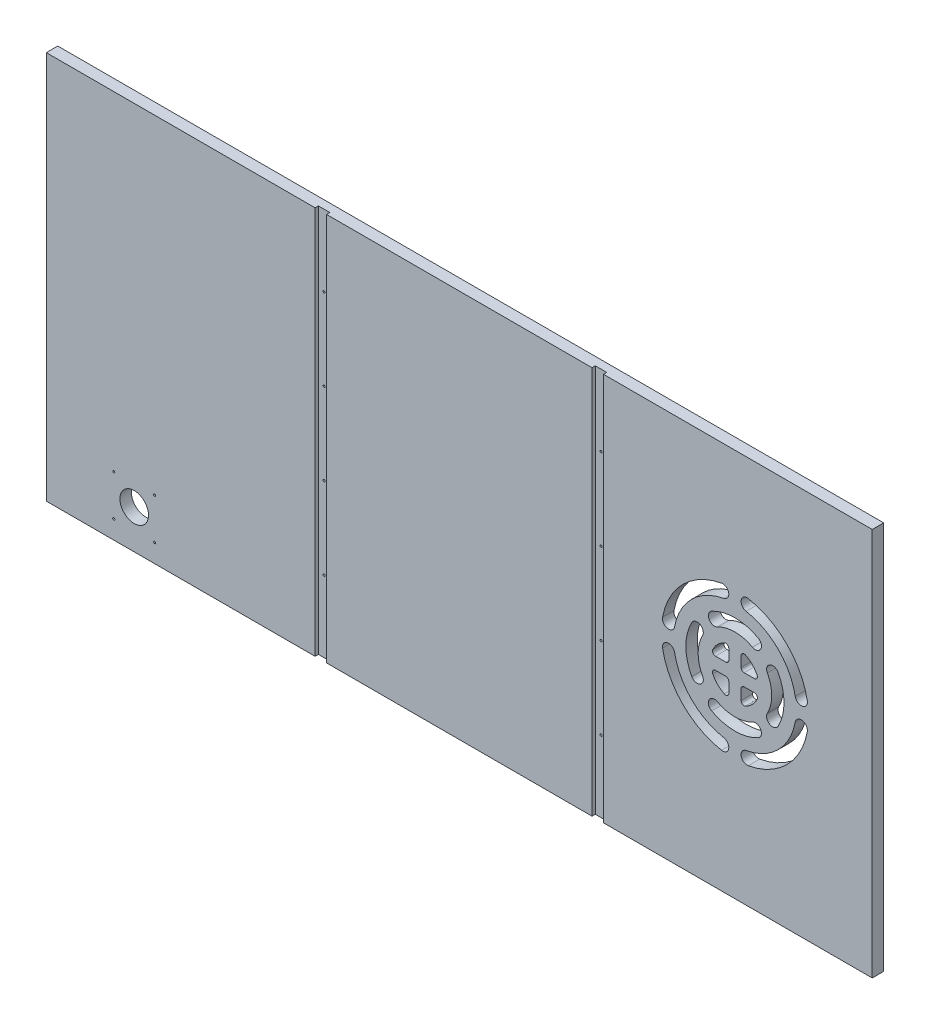
SolidWorks part; units mm, degrees
material "Pine"
ref_plane "Front Plane" through (0, 0, 0) normal (0, 0, 1) x (1, 0, 0)
ref_plane "Top Plane" through (0, 0, 0) normal (0, 1, 0) x (1, 0, 0)
ref_plane "Right Plane" through (0, 0, 0) normal (1, 0, 0) x (0, 0, -1)
sketch "Sketch1" plane through (0, 0, 0) normal (0, 0, 1) x (1, 0, 0)
  line L0 (8932.6508, -5243.5125) -> (10226.1458, -5243.5125)
  line L1 (9086.3208, -4722.0918) -> (10222.9708, -4853.7812)
  line L2 (8914.8708, -6342.0625) -> (10197.5708, -6342.0625)
  line L3 (8914.8708, -5808.6625) -> (10197.5708, -5808.6625)
  line L4 (8919.6333, -5253.0375) -> (10218.2083, -5253.0375)
  line L5 (9134.2633, -4656.1375) -> (9134.2633, -4638.3575)
  line L6 (9091.0833, -4638.3575) -> (9134.2633, -4638.3575)
  line L7 (9091.0833, -4567.2375) -> (9091.0833, -4638.3575)
  line L8 (9134.2633, -4656.1375) -> (9581.3033, -4656.1375)
  line L9 (9091.0833, -4567.2375) -> (9624.4833, -4567.2375)
  line L10 (9581.3033, -4656.1375) -> (9581.3033, -4638.3575)
  line L11 (9581.3033, -4638.3575) -> (9624.4833, -4638.3575)
  line L12 (9624.4833, -4567.2375) -> (9624.4833, -4638.3575)
  line L13 (8932.6508, -5225.7325) -> (9344.9775, -5225.7325)
  line L14 (8932.6508, -5256.2125) -> (8932.6508, -5243.5125)
  line L15 (8911.6958, -5256.2125) -> (8932.6508, -5256.2125)
  line L16 (8914.8708, -4722.0918) -> (9086.3208, -4722.0918)
  line L17 (8911.6958, -4715.5913) -> (8932.6508, -4715.5913)
  line L18 (8914.8708, -6342.0625) -> (8914.8708, -5808.6625)
  line L19 (12082.9917, -4722.0918) -> (10946.3417, -4853.7812)
  line L20 (12236.6617, -5243.5125) -> (10943.1667, -5243.5125)
  line L21 (10951.1042, -5253.0375) -> (12249.6792, -5253.0375)
  line L22 (10838.3917, -5656.2625) -> (11308.2917, -5656.2625)
  line L23 (10838.3917, -5719.7625) -> (11308.2917, -5719.7625)
  line L24 (10838.3917, -5742.5368) -> (11308.2917, -5742.5368)
  line L25 (10806.6417, -6342.0625) -> (11340.0417, -6342.0625)
  line L26 (10803.4667, -6335.7125) -> (11343.2167, -6335.7125)
  line L27 (10803.4667, -6317.9325) -> (11343.2167, -6317.9325)
  line L28 (10943.1667, -5225.7325) -> (11376.4483, -5225.7325)
  line L29 (11506.7292, -4754.5625) -> (10806.6417, -4827.5875)
  line L30 (11506.7292, -4567.2375) -> (11506.7292, -4754.5625)
  line L31 (10806.6417, -4567.2375) -> (10806.6417, -4827.5875)
  line L32 (10806.6417, -4567.2375) -> (11506.7292, -4567.2375)
  line L33 (10235.6708, -6329.3625) -> (10245.1958, -6329.3625)
  line L34 (10245.1958, -6329.3625) -> (10254.7208, -6278.5625)
  line L35 (10302.3458, -6329.3625) -> (10311.8708, -6278.5625)
  line L36 (10302.3458, -6329.3625) -> (10292.8208, -6329.3625)
  line L37 (10245.1958, -5821.3625) -> (10254.7208, -5872.1625)
  line L38 (10235.6708, -5821.3625) -> (10245.1958, -5821.3625)
  line L39 (10292.8208, -5821.3625) -> (10302.3458, -5821.3625)
  line L40 (10302.3458, -5821.3625) -> (10311.8708, -5872.1625)
  line L41 (10235.6708, -5821.3625) -> (10235.6708, -6329.3625)
  line L42 (10254.7208, -5872.1625) -> (10254.7208, -6278.5625)
  line L43 (10311.8708, -5872.1625) -> (10311.8708, -6278.5625)
  line L44 (10292.8208, -5821.3625) -> (10292.8208, -6329.3625)
  line L45 (8932.6508, -5225.7325) -> (8932.6508, -4715.5913)
  line L46 (8911.6958, -4715.5913) -> (8911.6958, -5256.2125)
  line L47 (8914.8708, -5248.275) -> (8914.8708, -4722.0918)
  line L48 (8919.6333, -5253.0375) -> (8914.8708, -5248.275)
  line L49 (8914.8708, -5145.0875) -> (8937.426, -5145.0875)
  line L50 (8914.8708, -5202.2375) -> (8937.426, -5202.2375)
  line L51 (10838.3917, -5656.2625) -> (10838.3917, -5719.7625)
  line L52 (10832.0417, -5736.1868) -> (10856.1717, -5736.1868)
  line L53 (10806.6417, -6342.0625) -> (10806.6417, -5818.7368)
  line L54 (10832.0417, -5649.9125) -> (10856.1717, -5649.9125)
  line L55 (10832.0417, -5726.1125) -> (10856.1717, -5726.1125)
  line L56 (10806.6417, -5818.7368) -> (10833.9015, -5818.7368)
  line L57 (10832.0417, -5806.0442) -> (10851.6815, -5806.0442)
  line L58 (10856.1717, -5801.5541) -> (10856.1717, -5736.1868)
  line L59 (10838.3917, -5814.2467) -> (10838.3917, -5742.5368)
  line L60 (10832.0417, -5806.0442) -> (10832.0417, -5736.1868)
  line L61 (10803.4667, -6317.9325) -> (10803.4667, -6335.7125)
  line L62 (10197.5708, -5808.6625) -> (10197.5708, -6342.0625)
  line L63 (9762.3842, -6348.4125) -> (9762.3842, -5802.3125)
  line L64 (9780.1642, -6348.4125) -> (9762.3842, -6348.4125)
  line L65 (9780.1642, -5802.3125) -> (9780.1642, -6348.4125)
  line L66 (9762.3842, -5802.3125) -> (9780.1642, -5802.3125)
  line L67 (9332.2775, -6348.4125) -> (9332.2775, -5802.3125)
  line L68 (9332.2775, -6348.4125) -> (9350.0575, -6348.4125)
  line L69 (9350.0575, -5802.3125) -> (9350.0575, -6348.4125)
  line L70 (9332.2775, -5802.3125) -> (9350.0575, -5802.3125)
  line L71 (9993.8374, -6061.075) -> (9993.8374, -6045.2418)
  line L72 (9998.5999, -6065.8375) -> (10014.4331, -6065.8375)
  line L73 (9998.5999, -6084.8875) -> (10014.4331, -6084.8875)
  line L74 (9993.8374, -6105.4832) -> (9993.8374, -6089.65)
  line L75 (9974.7874, -6105.4832) -> (9974.7874, -6089.65)
  line L76 (9954.1917, -6084.8875) -> (9970.0249, -6084.8875)
  line L77 (9974.7874, -6061.075) -> (9974.7874, -6045.2418)
  line L78 (9954.1917, -6065.8375) -> (9970.0249, -6065.8375)
  line L79 (10793.9417, -6237.2875) -> (10816.4969, -6237.2875)
  line L80 (10793.9417, -6294.4375) -> (10816.4969, -6294.4375)
  line L81 (10856.1717, -5649.9125) -> (10856.1717, -5726.1125)
  line L82 (10832.0417, -5726.1125) -> (10832.0417, -5649.9125)
  line L83 (10226.1458, -5225.7325) -> (10226.1458, -5243.5125)
  line L84 (10205.1908, -5257.8) -> (10205.1908, -4844.2499)
  line L85 (10230.9083, -4844.2499) -> (10230.9083, -5257.8)
  line L86 (10205.1908, -5257.8) -> (10230.9083, -5257.8)
  line L87 (10205.1908, -4844.2499) -> (10230.9083, -4844.2499)
  line L88 (10946.3417, -5176.8375) -> (10968.8969, -5176.8375)
  line L89 (9349.4676, -5141.9125) -> (9358.2674, -5141.9125)
  line L90 (10946.3417, -5119.6875) -> (10968.8969, -5119.6875)
  line L91 (9929.011, -4660.9635) -> (10066.0807, -4660.9635)
  line L92 (9929.011, -4678.7435) -> (10066.0807, -4678.7435)
  line L93 (10943.1667, -5225.7325) -> (10943.1667, -5243.5125)
  line L94 (10946.3417, -5248.275) -> (10951.1042, -5253.0375)
  line L95 (10946.3417, -5257.8063) -> (10946.3417, -4849.0188)
  line L96 (10964.1217, -5257.8) -> (10964.1217, -4844.2499)
  line L97 (10938.4042, -4844.2499) -> (10938.4042, -5257.8)
  line L98 (10938.4042, -5257.8) -> (10964.1217, -5257.8)
  line L99 (10964.1217, -4844.2499) -> (10938.4042, -4844.2499)
  line L100 (10344.8908, -4560.8875) -> (10369.0208, -4560.8875)
  line L101 (10344.8908, -4560.8875) -> (10369.0208, -4560.8875)
  line L102 (10800.2917, -4560.8875) -> (10824.4217, -4560.8875)
  line L103 (10200.4156, -5119.6875) -> (10222.9708, -5119.6875)
  line L104 (10200.4156, -5176.8375) -> (10222.9708, -5176.8375)
  line L105 (9344.9775, -5146.4026) -> (9344.9775, -5225.7325)
  line L106 (10344.8908, -4560.8875) -> (10344.8908, -4833.9375)
  line L107 (9792.8642, -5225.7325) -> (9792.8642, -5146.4026)
  line L108 (9362.7575, -5225.7325) -> (9775.0842, -5225.7325)
  line L109 (9680.3633, -4761.8396) -> (9680.3633, -4559.9604)
  line L110 (9656.2333, -4559.9604) -> (9680.3633, -4559.9604)
  line L111 (9656.2333, -4761.8396) -> (9680.3633, -4761.8396)
  line L112 (9656.2333, -4761.8396) -> (9656.2333, -4559.9604)
  line L113 (9779.5743, -5141.9125) -> (9788.374, -5141.9125)
  line L114 (10070.5708, -4665.4536) -> (10070.5708, -4674.2534)
  line L115 (9924.5208, -4674.2534) -> (9924.5208, -4665.4536)
  line L116 (12127.4417, -6188.3925) -> (12205.5015, -6188.3925)
  line L117 (12209.9917, -6170.6125) -> (12209.9917, -6183.9024)
  line L118 (9792.8642, -5225.7325) -> (10226.1458, -5225.7325)
  line L119 (9662.5833, -4754.5625) -> (10362.6708, -4827.5875)
  line L120 (9662.5833, -4567.2375) -> (9662.5833, -4754.5625)
  line L121 (10362.6708, -4567.2375) -> (10362.6708, -4827.5875)
  line L122 (9662.5833, -4567.2375) -> (10362.6708, -4567.2375)
  line L123 (10824.4217, -4833.9375) -> (10800.2917, -4833.9375)
  line L124 (10800.2917, -4833.9375) -> (10800.2917, -4560.8875)
  line L125 (10824.4217, -4560.8875) -> (10824.4217, -4833.9375)
  line L126 (10344.8908, -4833.9375) -> (10369.0208, -4833.9375)
  line L127 (10369.0208, -4833.9375) -> (10369.0208, -4560.8875)
  line L128 (10222.9708, -5248.275) -> (10218.2083, -5253.0375)
  line L129 (10222.9708, -5257.8063) -> (10222.9708, -4849.0188)
  line L130 (11734.6544, -5701.375) -> (11739.2301, -5701.375)
  line L131 (9362.7575, -5225.7325) -> (9362.7575, -5146.4026)
  line L132 (9775.0842, -5146.4026) -> (9775.0842, -5225.7325)
  line L133 (11761.3864, -5701.375) -> (11756.8282, -5701.375)
  line L134 (11734.6544, -5693.755) -> (11739.2301, -5693.755)
  line L135 (11761.4039, -5693.755) -> (11756.8282, -5693.755)
  line L136 (11734.6544, -5701.375) -> (11739.2301, -5701.375)
  line L137 (11744.3462, -5721.3024) -> (11744.3462, -5706.4179)
  line L138 (11751.7122, -5721.3024) -> (11751.7122, -5706.4179)
  line L139 (11740.0917, -6170.6125) -> (11740.0917, -6183.9024)
  line L140 (11689.2917, -6188.3925) -> (11822.6417, -6188.3925)
  line L141 (11689.2917, -6348.4093) -> (11689.2917, -6164.2657)
  line L142 (11689.2917, -6164.2657) -> (11746.4417, -6164.2657)
  line L143 (11746.4417, -6164.2657) -> (11746.4417, -6188.3925)
  line L144 (11689.2917, -6164.2657) -> (11746.4417, -6164.2657)
  line L145 (11340.0417, -5818.7368) -> (11340.0417, -6342.0625)
  line L146 (11290.5117, -5726.1125) -> (11314.6417, -5726.1125)
  line L147 (11290.5117, -5649.9125) -> (11290.5117, -5726.1125)
  line L148 (11340.0417, -5818.7368) -> (11312.7818, -5818.7368)
  line L149 (11314.6417, -5806.0442) -> (11295.0018, -5806.0442)
  line L150 (11290.5117, -5801.5541) -> (11290.5117, -5736.1868)
  line L151 (11308.2917, -5814.2467) -> (11308.2917, -5742.5368)
  line L152 (11314.6417, -5806.0442) -> (11314.6417, -5736.1868)
  line L153 (11290.5117, -5736.1868) -> (11314.6417, -5736.1868)
  line L154 (11848.0417, -6267.1325) -> (11962.3417, -6267.1325)
  line L155 (11962.3417, -6267.1325) -> (11962.3417, -6203.6325)
  line L156 (11343.2167, -6317.9325) -> (11343.2167, -6335.7125)
  line L157 (11365.4417, -5656.2625) -> (11365.4417, -5719.7625)
  line L158 (11365.4417, -5656.2625) -> (11479.7417, -5656.2625)
  line L159 (11778.1917, -6071.3937) -> (11802.3217, -6071.3937)
  line L160 (11314.6417, -5726.1125) -> (11314.6417, -5649.9125)
  line L161 (11314.6417, -5649.9125) -> (11290.5117, -5649.9125)
  line L162 (11308.2917, -5719.7625) -> (11308.2917, -5656.2625)
  line L163 (11689.2917, -6348.4093) -> (11713.4217, -6348.4093)
  line L164 (12203.6417, -6164.2657) -> (12260.7917, -6164.2657)
  line L165 (11713.4217, -6348.4093) -> (11713.4217, -6164.2657)
  line L166 (11695.6417, -6342.0625) -> (11695.6417, -6170.6125)
  line L167 (11695.6417, -6048.5337) -> (11699.4517, -6052.3437)
  line L168 (11822.6417, -6292.5325) -> (11822.6417, -6188.3925)
  line L169 (11695.6417, -6342.0625) -> (11695.6417, -6170.6125)
  line L170 (11848.0417, -6203.6325) -> (11962.3417, -6203.6325)
  line L171 (11848.0417, -6203.6325) -> (11848.0417, -6267.1325)
  line L172 (11987.7417, -6267.1325) -> (11987.7417, -6203.6325)
  line L173 (11784.5417, -6077.7437) -> (11784.5417, -6141.2438)
  line L174 (11517.8417, -5656.2625) -> (11632.1417, -5656.2625)
  line L175 (11632.1417, -5656.2625) -> (11632.1417, -5719.7625)
  line L176 (11632.1417, -5719.7625) -> (11517.8417, -5719.7625)
  line L177 (11517.8417, -5719.7625) -> (11517.8417, -5656.2625)
  line L178 (11692.4667, -6028.2137) -> (11692.4667, -6045.9937)
  line L179 (11695.6417, -5979.3188) -> (11718.1969, -5979.3188)
  line L180 (11695.6417, -5922.1687) -> (11718.1969, -5922.1687)
  line L181 (11821.0415, -5722.9375) -> (11821.0415, -5943.6)
  line L182 (11687.7042, -5651.5) -> (11701.9917, -5651.5)
  line L183 (11687.7042, -5651.5) -> (11687.7042, -6055.5251)
  line L184 (11687.7042, -6055.5251) -> (11701.9917, -6055.5251)
  line L185 (11701.9917, -6055.5251) -> (11701.9917, -5651.5)
  line L186 (11695.6417, -6055.2013) -> (11695.6417, -5649.595)
  line L187 (11695.6417, -5656.2625) -> (11695.6417, -6048.5337)
  line L188 (11695.6417, -6170.6125) -> (11740.0917, -6170.6125)
  line L189 (12203.6417, -6164.2657) -> (12203.6417, -6188.3925)
  line L190 (12254.4417, -6342.0625) -> (12254.4417, -6170.6125)
  line L191 (12129.0419, -5943.6) -> (12129.0419, -5722.9375)
  line L192 (12254.4417, -6048.5337) -> (12250.6317, -6052.3437)
  line L193 (12257.6167, -6045.9937) -> (12257.6167, -6028.2137)
  line L194 (12248.0917, -5651.5) -> (12262.3792, -5651.5)
  line L195 (12262.3792, -5651.5) -> (12262.3792, -6055.5251)
  line L196 (12262.3792, -6055.5251) -> (12248.0917, -6055.5251)
  line L197 (12248.0917, -6055.5251) -> (12248.0917, -5651.5)
  line L198 (12254.4417, -6141.2438) -> (12254.4417, -6077.7437)
  line L199 (12236.6617, -6164.2657) -> (12260.7917, -6164.2657)
  line L200 (12102.0417, -6267.1325) -> (11987.7417, -6267.1325)
  line L201 (11330.1865, -6237.2875) -> (11352.7417, -6237.2875)
  line L202 (11330.1865, -6294.4375) -> (11352.7417, -6294.4375)
  line L203 (11474.6617, -5851.8425) -> (11492.4417, -5851.8425)
  line L204 (11474.6617, -5808.6625) -> (11474.6617, -5851.8425)
  line L205 (11403.5417, -5808.6625) -> (11474.6617, -5808.6625)
  line L206 (11492.4417, -5851.8425) -> (11492.4417, -6298.8825)
  line L207 (11403.5417, -6342.0625) -> (11403.5417, -5808.6625)
  line L208 (11474.6617, -6298.8825) -> (11492.4417, -6298.8825)
  line L209 (11474.6617, -6342.0625) -> (11474.6617, -6298.8825)
  line L210 (11403.5417, -6342.0625) -> (11474.6617, -6342.0625)
  line L211 (11619.4417, -5851.8425) -> (11601.6617, -5851.8425)
  line L212 (11601.6617, -5808.6625) -> (11601.6617, -5851.8425)
  line L213 (11530.5417, -5808.6625) -> (11601.6617, -5808.6625)
  line L214 (11619.4417, -5851.8425) -> (11619.4417, -6298.8825)
  line L215 (11530.5417, -6342.0625) -> (11530.5417, -5808.6625)
  line L216 (11619.4417, -6298.8825) -> (11601.6617, -6298.8825)
  line L217 (11601.6617, -6342.0625) -> (11601.6617, -6298.8825)
  line L218 (11530.5417, -6342.0625) -> (11601.6617, -6342.0625)
  line L219 (11479.7417, -5719.7625) -> (11479.7417, -5656.2625)
  line L220 (11365.4417, -5719.7625) -> (11479.7417, -5719.7625)
  line L221 (11778.1917, -6147.5937) -> (11802.3217, -6147.5937)
  line L222 (11802.3217, -6071.3937) -> (11802.3217, -6147.5937)
  line L223 (11778.1917, -6147.5937) -> (11778.1917, -6071.3937)
  line L224 (12254.4417, -5922.1687) -> (12231.8865, -5922.1687)
  line L225 (12254.4417, -5979.3188) -> (12231.8865, -5979.3188)
  line L226 (12254.4417, -6055.2013) -> (12254.4417, -5649.595)
  line L227 (12254.4417, -6048.5337) -> (12254.4417, -5656.2625)
  line L228 (11841.6917, -5702.2873) -> (12108.3917, -5702.2873)
  line L229 (11822.6417, -6292.5325) -> (12127.4417, -6292.5325)
  line L230 (12127.4417, -6292.5325) -> (12127.4417, -6188.3925)
  line L231 (12254.4417, -6170.6125) -> (12209.9917, -6170.6125)
  line L232 (11695.6417, -6342.0625) -> (12254.4417, -6342.0625)
  line L233 (12236.6617, -6348.4093) -> (12260.7917, -6348.4093)
  line L234 (12260.7917, -6348.4093) -> (12260.7917, -6164.2657)
  line L235 (12236.6617, -6348.4093) -> (12236.6617, -6164.2657)
  line L236 (12102.0417, -6203.6325) -> (12102.0417, -6267.1325)
  line L237 (11987.7417, -6203.6325) -> (12102.0417, -6203.6325)
  line L238 (12236.6617, -6147.5937) -> (12236.6617, -6071.3937)
  line L239 (12203.6417, -6188.3925) -> (12260.7917, -6188.3925)
  line L240 (11098.7417, -4665.4536) -> (11098.7417, -4674.2534)
  line L241 (11394.2283, -5146.4026) -> (11394.2283, -5225.7325)
  line L242 (11376.4483, -5225.7325) -> (11376.4483, -5146.4026)
  line L243 (11394.2283, -5225.7325) -> (11806.555, -5225.7325)
  line L244 (11841.6917, -5964.2502) -> (12108.3917, -5964.2502)
  line L245 (12236.6617, -6147.5937) -> (12260.7917, -6147.5937)
  line L246 (12236.6617, -5256.2125) -> (12236.6617, -5243.5125)
  line L247 (12260.7917, -6147.5937) -> (12260.7917, -6071.3937)
  line L248 (12260.7917, -6071.3937) -> (12236.6617, -6071.3937)
  line L249 (12254.4417, -6077.7437) -> (11784.5417, -6077.7437)
  line L250 (11784.5417, -6141.2438) -> (12254.4417, -6141.2438)
  line L252 (12254.4417, -5656.2625) -> (11695.6417, -5656.2625)
  line L253 (11699.4517, -6052.3437) -> (12250.6317, -6052.3437)
  line L254 (11692.4667, -6045.9937) -> (12257.6167, -6045.9937)
  line L255 (11692.4667, -6028.2137) -> (12257.6167, -6028.2137)
  line L256 (11824.335, -5146.4026) -> (11824.335, -5225.7325)
  line L257 (11811.0451, -5141.9125) -> (11819.8449, -5141.9125)
  line L258 (11244.7917, -4674.2534) -> (11244.7917, -4665.4536)
  line L259 (11806.555, -5225.7325) -> (11806.555, -5146.4026)
  line L260 (11488.9492, -4761.8396) -> (11488.9492, -4559.9604)
  line L261 (11488.9492, -4559.9604) -> (11513.0792, -4559.9604)
  line L262 (11488.9492, -4761.8396) -> (11513.0792, -4761.8396)
  line L263 (11513.0792, -4761.8396) -> (11513.0792, -4559.9604)
  line L264 (11240.3015, -4660.9635) -> (11103.2318, -4660.9635)
  line L265 (11103.2318, -4678.7435) -> (11240.3015, -4678.7435)
  line L266 (12236.6617, -5225.7325) -> (12236.6617, -4715.5913)
  line L267 (12257.6167, -4715.5913) -> (12257.6167, -5256.2125)
  line L268 (12254.4417, -5248.275) -> (12254.4417, -4722.0918)
  line L269 (12236.6617, -5225.7325) -> (11824.335, -5225.7325)
  line L270 (12035.0492, -4656.1375) -> (12035.0492, -4638.3575)
  line L271 (12078.2292, -4638.3575) -> (12035.0492, -4638.3575)
  line L272 (12078.2292, -4567.2375) -> (12078.2292, -4638.3575)
  line L273 (12035.0492, -4656.1375) -> (11588.0092, -4656.1375)
  line L274 (11544.8292, -4567.2375) -> (12078.2292, -4567.2375)
  line L275 (11588.0092, -4656.1375) -> (11588.0092, -4638.3575)
  line L276 (11544.8292, -4638.3575) -> (11588.0092, -4638.3575)
  line L277 (11544.8292, -4567.2375) -> (11544.8292, -4638.3575)
  line L278 (12249.6792, -5253.0375) -> (12254.4417, -5248.275)
  line L280 (12257.6167, -5256.2125) -> (12236.6617, -5256.2125)
  line L281 (12231.8865, -5145.0875) -> (12254.4417, -5145.0875)
  line L282 (12231.8865, -5202.2375) -> (12254.4417, -5202.2375)
  line L283 (12236.6617, -4715.5913) -> (12257.6167, -4715.5913)
  line L284 (12082.9917, -4722.0918) -> (12254.4417, -4722.0918)
  line L285 (11380.9385, -5141.9125) -> (11389.7382, -5141.9125)
  circle A0 centre (8923.7608, -4778.9042) radius 1.5875
  circle A1 centre (9062.6598, -4736.3765) radius 2.3685
  circle A2 centre (9051.3958, -6281.7375) radius 22.225
  circle A3 centre (9083.1458, -6249.9875) radius 1.5875
  circle A4 centre (9083.1458, -6313.4875) radius 1.5875
  circle A5 centre (9019.6458, -6249.9875) radius 1.5875
  circle A6 centre (9019.6458, -6313.4875) radius 1.5875
  circle A7 centre (8972.3383, -5202.2375) radius 1.5875
  circle A8 centre (8923.7608, -5015.9708) radius 1.5875
  circle A9 centre (8923.7608, -5134.5042) radius 1.5875
  circle A10 centre (9054.5708, -5234.6225) radius 1.5875
  circle A11 centre (8923.7608, -4897.4375) radius 1.5875
  circle A12 centre (8972.3383, -5087.9375) radius 1.5875
  circle A13 centre (8972.3383, -5145.0875) radius 1.5875
  circle A14 centre (10847.2817, -5668.9625) radius 1.5875
  circle A15 centre (10847.2817, -5707.0625) radius 1.5875
  circle A16 centre (10847.2817, -5755.2368) radius 1.5875
  circle A17 centre (10851.4092, -6237.2875) radius 1.5875
  circle A18 centre (10851.4092, -6294.4375) radius 1.5875
  circle A19 centre (10847.2817, -5793.3442) radius 1.5875
  arc A20 (10833.9015, -5818.7368) -> (10838.3917, -5814.2467) centre (10836.1466, -5816.4918) ccw
  arc A21 (10851.6815, -5806.0442) -> (10856.1717, -5801.5541) centre (10853.9266, -5803.7992) ccw
  circle A22 centre (10882.8417, -6040.4375) radius 1.5875
  circle A23 centre (10882.8417, -6218.2375) radius 1.5875
  circle A24 centre (10882.8417, -5862.6375) radius 1.5875
  circle A25 centre (10908.2417, -6326.8225) radius 1.5875
  circle A26 centre (10908.2417, -6326.8225) radius 1.5875
  circle A27 centre (10851.4092, -6180.1375) radius 1.5875
  circle A28 centre (10815.5317, -4783.4231) radius 1.5875
  circle A29 centre (10815.5317, -4696.9488) radius 1.5875
  circle A30 centre (10815.5317, -4610.4746) radius 1.5875
  circle A31 centre (10979.1323, -4867.0082) radius 2.3685
  circle A32 centre (10190.1802, -4867.0082) radius 2.3685
  circle A33 centre (10955.2317, -4929.9812) radius 1.5875
  circle A34 centre (10955.2317, -5031.5812) radius 1.5875
  circle A35 centre (10214.0808, -4929.9812) radius 1.5875
  circle A36 centre (10214.0808, -5031.5812) radius 1.5875
  circle A37 centre (9341.1675, -6265.8625) radius 1.5875
  circle A38 centre (9771.2742, -5884.8625) radius 1.5875
  circle A39 centre (9771.2742, -6138.8625) radius 1.5875
  circle A40 centre (9771.2742, -6011.8625) radius 1.5875
  arc A41 (10036.2287, -6113.8083) -> (10051.3426, -6111.6033) centre (10042.9639, -6107.0732) ccw
  arc A42 (10051.3426, -6111.6033) -> (10051.3426, -6039.1217) centre (9984.3124, -6075.3625) ccw
  arc A43 (10051.3426, -6039.1217) -> (10036.2287, -6036.9167) centre (10042.9639, -6043.6518) ccw
  arc A44 (10034.5851, -6102.5431) -> (10034.5851, -6048.1819) centre (9984.3124, -6075.3625) ccw
  arc A45 (10034.5851, -6102.5431) -> (10036.2287, -6113.8083) centre (10042.9639, -6107.0732) ccw
  arc A46 (10036.2287, -6036.9167) -> (10034.5851, -6048.1819) centre (10042.9639, -6043.6518) ccw
  arc A47 (9945.8666, -6127.2787) -> (9948.0717, -6142.3927) centre (9952.6018, -6134.0139) ccw
  arc A48 (9948.0717, -6142.3927) -> (10020.5532, -6142.3927) centre (9984.3124, -6075.3625) ccw
  arc A49 (10020.5532, -6142.3927) -> (10022.7583, -6127.2787) centre (10016.0231, -6134.0139) ccw
  arc A50 (9957.1319, -6125.6352) -> (10011.493, -6125.6352) centre (9984.3124, -6075.3625) ccw
  arc A51 (9957.1319, -6125.6352) -> (9945.8666, -6127.2787) centre (9952.6018, -6134.0139) ccw
  arc A52 (10022.7583, -6127.2787) -> (10011.493, -6125.6352) centre (10016.0231, -6134.0139) ccw
  arc A53 (9932.3962, -6036.9167) -> (9917.2822, -6039.1217) centre (9925.661, -6043.6518) ccw
  arc A54 (9917.2822, -6039.1217) -> (9917.2822, -6111.6033) centre (9984.3124, -6075.3625) ccw
  arc A55 (9917.2822, -6111.6033) -> (9932.3962, -6113.8083) centre (9925.661, -6107.0732) ccw
  arc A56 (9934.0398, -6048.1819) -> (9934.0398, -6102.5431) centre (9984.3124, -6075.3625) ccw
  arc A57 (9934.0398, -6048.1819) -> (9932.3962, -6036.9167) centre (9925.661, -6043.6518) ccw
  arc A58 (9932.3962, -6113.8083) -> (9934.0398, -6102.5431) centre (9925.661, -6107.0732) ccw
  arc A59 (9945.8666, -6023.4463) -> (9957.1319, -6025.0898) centre (9952.6018, -6016.7111) ccw
  arc A60 (10011.493, -6025.0898) -> (10022.7583, -6023.4463) centre (10016.0231, -6016.7111) ccw
  arc A61 (10011.493, -6025.0898) -> (9957.1319, -6025.0898) centre (9984.3124, -6075.3625) ccw
  arc A62 (9948.0717, -6008.3323) -> (9945.8666, -6023.4463) centre (9952.6018, -6016.7111) ccw
  arc A63 (10020.5532, -6008.3323) -> (9948.0717, -6008.3323) centre (9984.3124, -6075.3625) ccw
  arc A64 (10022.7583, -6023.4463) -> (10020.5532, -6008.3323) centre (10016.0231, -6016.7111) ccw
  arc A65 (10005.0943, -6187.7574) -> (10096.7073, -6096.1443) centre (9984.3124, -6075.3625) ccw
  arc A66 (9993.8374, -6178.3911) -> (10005.0943, -6187.7574) centre (10003.3624, -6178.3911) ccw
  arc A67 (10001.6306, -6169.0249) -> (10077.9748, -6092.6807) centre (9984.3124, -6075.3625) ccw
  arc A68 (10087.3411, -6084.8875) -> (10077.9748, -6092.6807) centre (10087.3411, -6094.4125) ccw
  arc A69 (10001.6306, -6169.0249) -> (9993.8374, -6178.3911) centre (10003.3624, -6178.3911) ccw
  arc A70 (9963.5306, -6187.7574) -> (9974.7874, -6178.3911) centre (9965.2624, -6178.3911) ccw
  arc A71 (9871.9176, -6096.1443) -> (9963.5306, -6187.7574) centre (9984.3124, -6075.3625) ccw
  arc A72 (9881.2838, -6084.8875) -> (9871.9176, -6096.1443) centre (9881.2838, -6094.4125) ccw
  arc A73 (9890.65, -6092.6807) -> (9966.9943, -6169.0249) centre (9984.3124, -6075.3625) ccw
  arc A74 (9974.7874, -6178.3911) -> (9966.9943, -6169.0249) centre (9965.2624, -6178.3911) ccw
  arc A75 (9890.65, -6092.6807) -> (9881.2838, -6084.8875) centre (9881.2838, -6094.4125) ccw
  arc A76 (9871.9176, -6054.5807) -> (9881.2838, -6065.8375) centre (9881.2838, -6056.3125) ccw
  arc A77 (9963.5306, -5962.9676) -> (9871.9176, -6054.5807) centre (9984.3124, -6075.3625) ccw
  arc A78 (9974.7874, -5972.3339) -> (9963.5306, -5962.9676) centre (9965.2624, -5972.3339) ccw
  arc A79 (9966.9943, -5981.7001) -> (9890.65, -6058.0443) centre (9984.3124, -6075.3625) ccw
  arc A80 (9881.2838, -6065.8375) -> (9890.65, -6058.0443) centre (9881.2838, -6056.3125) ccw
  arc A81 (9966.9943, -5981.7001) -> (9974.7874, -5972.3339) centre (9965.2624, -5972.3339) ccw
  arc A82 (10077.9748, -6058.0443) -> (10087.3411, -6065.8375) centre (10087.3411, -6056.3125) ccw
  arc A83 (9993.8374, -5972.3339) -> (10001.6306, -5981.7001) centre (10003.3624, -5972.3339) ccw
  arc A84 (10077.9748, -6058.0443) -> (10001.6306, -5981.7001) centre (9984.3124, -6075.3625) ccw
  arc A85 (10087.3411, -6065.8375) -> (10096.7073, -6054.5807) centre (10087.3411, -6056.3125) ccw
  arc A86 (10096.7073, -6054.5807) -> (10005.0943, -5962.9676) centre (9984.3124, -6075.3625) ccw
  arc A87 (10005.0943, -5962.9676) -> (9993.8374, -5972.3339) centre (10003.3624, -5972.3339) ccw
  arc A88 (10014.4331, -6065.8375) -> (10018.7361, -6059.0339) centre (10014.4331, -6061.075) ccw
  arc A89 (10018.7361, -6059.0339) -> (10000.641, -6040.9388) centre (9984.3124, -6075.3625) ccw
  arc A90 (10000.641, -6040.9388) -> (9993.8374, -6045.2418) centre (9998.5999, -6045.2418) ccw
  arc A91 (9993.8374, -6061.075) -> (9998.5999, -6065.8375) centre (9998.5999, -6061.075) ccw
  arc A92 (9993.8374, -6105.4832) -> (10000.641, -6109.7862) centre (9998.5999, -6105.4832) ccw
  arc A93 (10000.641, -6109.7862) -> (10018.7361, -6091.6911) centre (9984.3124, -6075.3625) ccw
  arc A94 (10018.7361, -6091.6911) -> (10014.4331, -6084.8875) centre (10014.4331, -6089.65) ccw
  arc A95 (9998.5999, -6084.8875) -> (9993.8374, -6089.65) centre (9998.5999, -6089.65) ccw
  arc A96 (9954.1917, -6084.8875) -> (9949.8888, -6091.6911) centre (9954.1917, -6089.65) ccw
  arc A97 (9949.8888, -6091.6911) -> (9967.9839, -6109.7862) centre (9984.3124, -6075.3625) ccw
  arc A98 (9967.9839, -6109.7862) -> (9974.7874, -6105.4832) centre (9970.0249, -6105.4832) ccw
  arc A99 (9974.7874, -6089.65) -> (9970.0249, -6084.8875) centre (9970.0249, -6089.65) ccw
  arc A100 (9970.0249, -6065.8375) -> (9974.7874, -6061.075) centre (9970.0249, -6061.075) ccw
  arc A101 (9949.8888, -6059.0339) -> (9954.1917, -6065.8375) centre (9954.1917, -6061.075) ccw
  arc A102 (9967.9839, -6040.9388) -> (9949.8888, -6059.0339) centre (9984.3124, -6075.3625) ccw
  arc A103 (9974.7874, -6045.2418) -> (9967.9839, -6040.9388) centre (9970.0249, -6045.2418) ccw
  arc A104 (10096.7073, -6096.1443) -> (10087.3411, -6084.8875) centre (10087.3411, -6094.4125) ccw
  circle A105 centre (9771.2742, -6265.8625) radius 1.5875
  circle A106 centre (9341.1675, -5884.8625) radius 1.5875
  circle A107 centre (9341.1675, -6138.8625) radius 1.5875
  circle A108 centre (9341.1675, -6011.8625) radius 1.5875
  circle A109 centre (11037.2315, -4887.5494) radius 15.0812
  arc A110 (9349.4676, -5141.9125) -> (9344.9775, -5146.4026) centre (9347.2226, -5144.1576) ccw
  arc A111 (9362.7575, -5146.4026) -> (9358.2674, -5141.9125) centre (9360.5124, -5144.1576) ccw
  circle A112 centre (9946.7458, -4669.8535) radius 1.5875
  arc A113 (9924.5208, -4674.2534) -> (9929.011, -4678.7435) centre (9926.7659, -4676.4984) ccw
  circle A114 centre (11003.8092, -5176.8375) radius 1.5875
  circle A115 centre (11003.8092, -5119.6875) radius 1.5875
  circle A116 centre (10353.7808, -4696.9488) radius 1.5875
  circle A117 centre (10353.7808, -4610.4746) radius 1.5875
  circle A118 centre (10353.7808, -4783.4231) radius 1.5875
  circle A119 centre (11003.8092, -5062.5375) radius 1.5875
  circle A120 centre (9353.8675, -5160.9625) radius 1.5875
  circle A121 centre (9638.7708, -5234.6225) radius 1.5875
  circle A122 centre (9671.4733, -4724.1144) radius 1.5875
  circle A123 centre (9671.4733, -4661.3637) radius 1.5875
  circle A124 centre (9671.4733, -4598.6129) radius 1.5875
  arc A125 (9792.8642, -5146.4026) -> (9788.374, -5141.9125) centre (9790.6191, -5144.1576) ccw
  arc A126 (9779.5743, -5141.9125) -> (9775.0842, -5146.4026) centre (9777.3292, -5144.1576) ccw
  circle A127 centre (10048.3458, -4669.8535) radius 1.5875
  arc A128 (10070.5708, -4665.4536) -> (10066.0807, -4660.9635) centre (10068.3258, -4663.2086) ccw
  arc A129 (10066.0807, -4678.7435) -> (10070.5708, -4674.2534) centre (10068.3258, -4676.4984) ccw
  circle A130 centre (9997.5458, -4669.8535) radius 1.5875
  arc A131 (9929.011, -4660.9635) -> (9924.5208, -4665.4536) centre (9926.7659, -4663.2086) ccw
  circle A132 centre (10132.081, -4887.5494) radius 15.0812
  circle A133 centre (10165.5033, -5176.8375) radius 1.5875
  circle A134 centre (10165.5033, -5119.6875) radius 1.5875
  circle A135 centre (9486.3708, -5234.6225) radius 1.5875
  circle A136 centre (10165.5033, -5062.5375) radius 1.5875
  circle A137 centre (9206.9708, -5234.6225) radius 1.5875
  circle A138 centre (10070.5708, -5234.6225) radius 1.5875
  circle A139 centre (9918.1708, -5234.6225) radius 1.5875
  circle A140 centre (9783.9742, -5160.9625) radius 1.5875
  circle A141 centre (9783.9742, -5193.9825) radius 1.5875
  circle A142 centre (9353.8675, -5193.9825) radius 1.5875
  circle A143 centre (11073.3417, -6326.8225) radius 1.5875
  circle A144 centre (11073.3417, -6326.8225) radius 1.5875
  circle A145 centre (11295.2742, -6180.1375) radius 1.5875
  circle A146 centre (11295.2742, -6294.4375) radius 1.5875
  circle A147 centre (11295.2742, -6237.2875) radius 1.5875
  circle A148 centre (11975.0417, -5692.775) radius 3.4925
  circle A149 centre (11263.8417, -5862.6375) radius 1.5875
  arc A150 (11739.2301, -5701.375) -> (11744.3462, -5706.4179) centre (11748.0292, -5697.565) ccw
  arc A151 (11751.7122, -5706.4179) -> (11756.8282, -5701.375) centre (11748.0292, -5697.565) ccw
  arc A152 (11744.3462, -5721.3024) -> (11751.7122, -5721.3024) centre (11748.0292, -5725.505) ccw
  arc A153 (11734.6544, -5693.755) -> (11724.9787, -5697.565) centre (11730.5667, -5697.565) ccw
  arc A154 (11756.8282, -5693.755) -> (11739.2301, -5693.755) centre (11748.0292, -5697.565) ccw
  arc A155 (11724.9787, -5697.565) -> (11734.6544, -5701.375) centre (11730.5667, -5697.565) ccw
  arc A156 (11761.3864, -5701.375) -> (11771.0797, -5697.565) centre (11765.4842, -5697.565) ccw
  arc A157 (11771.0797, -5697.565) -> (11761.4039, -5693.755) centre (11765.4917, -5697.565) ccw
  arc A158 (11740.0917, -6183.9024) -> (11744.5818, -6188.3925) centre (11742.3367, -6186.1474) ccw
  arc A159 (12205.5015, -6188.3925) -> (12209.9917, -6183.9024) centre (12207.7466, -6186.1474) ccw
  circle A160 centre (11299.4017, -5793.3442) radius 1.5875
  arc A161 (11308.2917, -5814.2467) -> (11312.7818, -5818.7368) centre (11310.5367, -5816.4918) ccw
  arc A162 (11290.5117, -5801.5541) -> (11295.0018, -5806.0442) centre (11292.7567, -5803.7992) ccw
  circle A163 centre (11704.5317, -6314.149) radius 1.5875
  circle A164 centre (11748.9817, -6208.7125) radius 1.5875
  circle A165 centre (11263.8417, -6218.2375) radius 1.5875
  circle A166 centre (11263.8417, -6040.4375) radius 1.5875
  circle A167 centre (11238.4417, -6326.8225) radius 1.5875
  circle A168 centre (11238.4417, -6326.8225) radius 1.5875
  circle A169 centre (11299.4017, -5668.9625) radius 1.5875
  circle A170 centre (11299.4017, -5707.0625) radius 1.5875
  circle A171 centre (11726.7567, -6179.5025) radius 1.5875
  circle A172 centre (11704.5317, -6199.3198) radius 1.5875
  circle A173 centre (11748.9817, -6272.2125) radius 1.5875
  circle A174 centre (11704.5317, -6256.7344) radius 1.5875
  circle A175 centre (11299.4017, -5755.2368) radius 1.5875
  circle A176 centre (11913.4467, -6301.4225) radius 1.5875
  circle A177 centre (11790.2567, -6301.4225) radius 1.5875
  circle A178 centre (11793.4317, -6128.5437) radius 1.5875
  circle A179 centre (11753.1092, -5865.0188) radius 1.5875
  circle A180 centre (11809.9417, -6037.1038) radius 1.5875
  circle A181 centre (11809.9417, -6037.1038) radius 1.5875
  circle A182 centre (11753.1092, -5922.1687) radius 1.5875
  circle A183 centre (11975.0417, -5973.7625) radius 3.4925
  circle A184 centre (11975.0417, -6037.1038) radius 1.5875
  circle A185 centre (11753.1092, -5979.3188) radius 1.5875
  circle A186 centre (11975.0417, -6037.1038) radius 1.5875
  arc A187 (11841.6917, -5702.2873) -> (11821.0415, -5722.9375) centre (11841.6917, -5722.9375) ccw
  circle A188 centre (11811.5292, -5833.2687) radius 3.4925
  arc A189 (11821.0415, -5943.6) -> (11841.6917, -5964.2502) centre (11841.6917, -5943.6) ccw
  circle A190 centre (12196.9742, -5865.0188) radius 1.5875
  arc A191 (12129.0419, -5722.9375) -> (12108.3917, -5702.2873) centre (12108.3917, -5722.9375) ccw
  circle A192 centre (12036.6367, -6301.4225) radius 1.5875
  circle A193 centre (12159.8267, -6301.4225) radius 1.5875
  circle A194 centre (12138.5542, -5833.2687) radius 3.4925
  circle A195 centre (12197.2917, -5761.0375) radius 15.0812
  circle A196 centre (11793.4317, -6090.4437) radius 1.5875
  circle A197 centre (12196.9742, -5922.1687) radius 1.5875
  arc A198 (12108.3917, -5964.2502) -> (12129.0419, -5943.6) centre (12108.3917, -5943.6) ccw
  circle A199 centre (12196.9742, -5979.3188) radius 1.5875
  circle A200 centre (12201.1017, -6272.2125) radius 1.5875
  circle A201 centre (12245.5517, -6314.149) radius 1.5875
  circle A202 centre (12245.5517, -6256.7344) radius 1.5875
  circle A203 centre (12201.1017, -6208.7125) radius 1.5875
  circle A204 centre (12223.3267, -6179.5025) radius 1.5875
  circle A205 centre (12245.5517, -6199.3198) radius 1.5875
  circle A206 centre (11171.7667, -4669.8535) radius 1.5875
  circle A207 centre (11222.5667, -4669.8535) radius 1.5875
  arc A208 (11240.3015, -4678.7435) -> (11244.7917, -4674.2534) centre (11242.5466, -4676.4984) ccw
  circle A209 centre (11385.3383, -5193.9825) radius 1.5875
  circle A210 centre (12106.6527, -4736.3765) radius 2.3685
  circle A211 centre (12140.1417, -6037.1038) radius 1.5875
  circle A212 centre (12140.1417, -6037.1038) radius 1.5875
  circle A213 centre (12245.5517, -6090.4437) radius 1.5875
  circle A214 centre (12245.5517, -6128.5437) radius 1.5875
  circle A215 centre (11385.3383, -5160.9625) radius 1.5875
  arc A216 (11824.335, -5146.4026) -> (11819.8449, -5141.9125) centre (11822.0899, -5144.1576) ccw
  arc A217 (11811.0451, -5141.9125) -> (11806.555, -5146.4026) centre (11808.8001, -5144.1576) ccw
  circle A218 centre (11815.445, -5193.9825) radius 1.5875
  circle A219 centre (11815.445, -5160.9625) radius 1.5875
  circle A220 centre (11530.5417, -5234.6225) radius 1.5875
  circle A221 centre (11962.3417, -5234.6225) radius 1.5875
  arc A222 (11244.7917, -4665.4536) -> (11240.3015, -4660.9635) centre (11242.5466, -4663.2086) ccw
  circle A223 centre (11682.9417, -5234.6225) radius 1.5875
  circle A224 centre (11497.8392, -4724.1144) radius 1.5875
  circle A225 centre (11497.8392, -4661.3637) radius 1.5875
  circle A226 centre (11497.8392, -4598.6129) radius 1.5875
  circle A227 centre (11120.9667, -4669.8535) radius 1.5875
  arc A228 (11103.2318, -4660.9635) -> (11098.7417, -4665.4536) centre (11100.9867, -4663.2086) ccw
  arc A229 (11098.7417, -4674.2534) -> (11103.2318, -4678.7435) centre (11100.9867, -4676.4984) ccw
  circle A230 centre (12196.9742, -5202.2375) radius 1.5875
  circle A231 centre (12245.5517, -5015.9708) radius 1.5875
  circle A232 centre (12245.5517, -5134.5042) radius 1.5875
  circle A233 centre (12114.7417, -5234.6225) radius 1.5875
  circle A234 centre (12245.5517, -4897.4375) radius 1.5875
  circle A235 centre (12245.5517, -4778.9042) radius 1.5875
  circle A236 centre (12196.9742, -5087.9375) radius 1.5875
  circle A237 centre (12196.9742, -5145.0875) radius 1.5875
  circle A238 centre (11098.7417, -5234.6225) radius 1.5875
  circle A239 centre (11251.1417, -5234.6225) radius 1.5875
  arc A240 (11380.9385, -5141.9125) -> (11376.4483, -5146.4026) centre (11378.6934, -5144.1576) ccw
  arc A241 (11394.2283, -5146.4026) -> (11389.7382, -5141.9125) centre (11391.9833, -5144.1576) ccw
sketch "CabBottom_Outline" plane through (0, 0, 0) normal (0, 0, 1) x (1, 0, 0)
  line L0 (8914.8708, -6376.9875) -> (10197.5708, -6376.9875)
  line L1 (10197.5708, -6376.9875) -> (10197.5708, -5773.7375)
  line L2 (10197.5708, -5773.7375) -> (8914.8708, -5773.7375)
  line L3 (8914.8708, -5773.7375) -> (8914.8708, -6376.9875)
  line L4 (8914.8708, -6075.3625) -> (10197.5708, -6075.3625) construction
  dimension "CabBottom_Width" = 603.25
  dimension "CabBottom_Length" = 1282.7
extrude "CabBottom_Thickness" add sketch "CabBottom_Outline" against normal blind 17.78
sketch "Sketch4" plane through (0, 0, 0) normal (0, 0, 1) x (1, 0, 0)
  line L0 (9974.7874, -6061.075) -> (9974.7874, -6045.2418)
  line L1 (9954.1917, -6065.8375) -> (9970.0249, -6065.8375)
  line L2 (9993.8374, -6045.2418) -> (9993.8374, -6061.075)
  line L3 (9998.5999, -6065.8375) -> (10014.4331, -6065.8375)
  line L4 (10014.4331, -6084.8875) -> (9998.5999, -6084.8875)
  line L5 (9993.8374, -6089.65) -> (9993.8374, -6105.4832)
  line L6 (9970.0249, -6084.8875) -> (9954.1917, -6084.8875)
  line L7 (9974.7874, -6105.4832) -> (9974.7874, -6089.65)
  line L8 (8914.8708, -6376.9875) -> (10197.5708, -6376.9875) construction
  line L9 (8914.8708, -5773.7375) -> (8914.8708, -6376.9875) construction
  line L10 (9019.6458, -6348.4125) -> (9083.1458, -6348.4125) construction
  line L11 (9083.1458, -6348.4125) -> (9083.1458, -6284.9125) construction
  line L12 (9083.1458, -6284.9125) -> (9019.6458, -6284.9125) construction
  line L13 (9019.6458, -6284.9125) -> (9019.6458, -6348.4125) construction
  arc A0 (9890.65, -6058.0443) -> (9966.9943, -5981.7001) centre (9984.3124, -6075.3625) cw
  arc A1 (9966.9943, -5981.7001) -> (9890.65, -6058.0443) centre (9984.3124, -6075.3625) ccw construction
  arc A2 (9966.9943, -5981.7001) -> (9974.7874, -5972.3339) centre (9965.2624, -5972.3339) ccw
  arc A3 (9974.7874, -5972.3339) -> (9963.5306, -5962.9676) centre (9965.2624, -5972.3339) ccw
  arc A4 (9963.5306, -5962.9676) -> (9871.9176, -6054.5807) centre (9984.3124, -6075.3625) ccw
  arc A5 (9871.9176, -6054.5807) -> (9890.65, -6058.0443) centre (9881.2838, -6056.3125) ccw
  arc A6 (9890.65, -6092.6807) -> (9966.9943, -6169.0249) centre (9984.3124, -6075.3625) ccw
  arc A7 (9974.7874, -6178.3911) -> (9966.9943, -6169.0249) centre (9965.2624, -6178.3911) ccw construction
  arc A8 (10001.6306, -6169.0249) -> (10077.9748, -6092.6807) centre (9984.3124, -6075.3625) ccw
  arc A9 (10087.3411, -6084.8875) -> (10077.9748, -6092.6807) centre (10087.3411, -6094.4125) ccw construction
  arc A10 (10001.6306, -5981.7001) -> (10077.9748, -6058.0443) centre (9984.3124, -6075.3625) cw
  arc A11 (10077.9748, -6058.0443) -> (10087.3411, -6065.8375) centre (10087.3411, -6056.3125) ccw construction
  arc A12 (9890.65, -6092.6807) -> (9871.9176, -6096.1443) centre (9881.2838, -6094.4125) ccw
  arc A13 (9871.9176, -6096.1443) -> (9963.5306, -6187.7574) centre (9984.3124, -6075.3625) ccw
  arc A14 (9963.5306, -6187.7574) -> (9966.9943, -6169.0249) centre (9965.2624, -6178.3911) ccw
  arc A15 (10001.6306, -6169.0249) -> (10005.0943, -6187.7574) centre (10003.3624, -6178.3911) ccw
  arc A16 (10005.0943, -6187.7574) -> (10096.7073, -6096.1443) centre (9984.3124, -6075.3625) ccw
  arc A17 (10096.7073, -6096.1443) -> (10077.9748, -6092.6807) centre (10087.3411, -6094.4125) ccw
  arc A18 (10077.9748, -6058.0443) -> (10096.7073, -6054.5807) centre (10087.3411, -6056.3125) ccw
  arc A19 (10096.7073, -6054.5807) -> (10005.0943, -5962.9676) centre (9984.3124, -6075.3625) ccw
  arc A20 (10005.0943, -5962.9676) -> (10001.6306, -5981.7001) centre (10003.3624, -5972.3339) ccw
  arc A21 (9917.2822, -6111.6033) -> (9917.2822, -6039.1217) centre (9984.3124, -6075.3625) cw
  arc A22 (9932.3962, -6036.9167) -> (9917.2822, -6039.1217) centre (9925.661, -6043.6518) ccw construction
  arc A23 (9948.0717, -6008.3323) -> (10020.5532, -6008.3323) centre (9984.3124, -6075.3625) cw
  arc A25 (9948.0717, -6008.3323) -> (9957.1319, -6025.0898) centre (9952.6018, -6016.7111) ccw
  arc A28 (10020.5532, -6142.3927) -> (9948.0717, -6142.3927) centre (9984.3124, -6075.3625) cw
  arc A30 (9948.0717, -6142.3927) -> (10020.5532, -6142.3927) centre (9984.3124, -6075.3625) ccw construction
  arc A31 (9917.2822, -6039.1217) -> (9934.0398, -6048.1819) centre (9925.661, -6043.6518) cw
  arc A32 (9934.0398, -6048.1819) -> (9934.0398, -6102.5431) centre (9984.3124, -6075.3625) ccw
  arc A33 (9934.0398, -6102.5431) -> (9917.2822, -6111.6033) centre (9925.661, -6107.0732) cw
  arc A34 (9948.0717, -6142.3927) -> (9957.1319, -6125.6352) centre (9952.6018, -6134.0139) cw
  arc A35 (9957.1319, -6125.6352) -> (10011.493, -6125.6352) centre (9984.3124, -6075.3625) ccw
  arc A36 (10011.493, -6125.6352) -> (10020.5532, -6142.3927) centre (10016.0231, -6134.0139) cw
  arc A37 (9957.1319, -6025.0898) -> (10011.493, -6025.0898) centre (9984.3124, -6075.3625) cw
  arc A38 (10051.3426, -6039.1217) -> (10051.3426, -6111.6033) centre (9984.3124, -6075.3625) cw
  arc A39 (10036.2287, -6113.8083) -> (10051.3426, -6111.6033) centre (10042.9639, -6107.0732) ccw construction
  arc A40 (10051.3426, -6111.6033) -> (10034.5851, -6102.5431) centre (10042.9638, -6107.0732) cw
  arc A41 (10051.3426, -6039.1217) -> (10034.6383, -6048.1322) centre (10042.9948, -6043.6351) ccw
  arc A42 (10034.6383, -6048.1322) -> (10034.5851, -6102.5431) centre (9984.1765, -6075.2883) cw
  arc A43 (10020.5532, -6008.3323) -> (10011.493, -6025.0898) centre (10016.0231, -6016.7111) cw
  arc A44 (9974.7874, -6045.2418) -> (9967.9839, -6040.9388) centre (9970.0249, -6045.2418) ccw
  arc A45 (9967.9839, -6040.9388) -> (9949.8888, -6059.0339) centre (9984.3124, -6075.3625) ccw
  arc A46 (9949.8888, -6059.0339) -> (9954.1917, -6065.8375) centre (9954.1917, -6061.075) ccw
  arc A47 (9970.0249, -6065.8375) -> (9974.7874, -6061.075) centre (9970.0249, -6061.075) ccw
  arc A48 (9993.8374, -6061.075) -> (9998.5999, -6065.8375) centre (9998.5999, -6061.075) ccw
  arc A49 (10014.4331, -6065.8375) -> (10018.7361, -6059.0339) centre (10014.4331, -6061.075) ccw
  arc A50 (10018.7361, -6059.0339) -> (10000.641, -6040.9388) centre (9984.3124, -6075.3625) ccw
  arc A51 (10000.641, -6040.9388) -> (9993.8374, -6045.2418) centre (9998.5999, -6045.2418) ccw
  arc A52 (9998.5999, -6084.8875) -> (9993.8374, -6089.65) centre (9998.5999, -6089.65) ccw
  arc A53 (9993.8374, -6105.4832) -> (10000.641, -6109.7862) centre (9998.5999, -6105.4832) ccw
  arc A54 (10000.641, -6109.7862) -> (10018.7361, -6091.6911) centre (9984.3124, -6075.3625) ccw
  arc A55 (10018.7361, -6091.6911) -> (10014.4331, -6084.8875) centre (10014.4331, -6089.65) ccw
  arc A56 (9954.1917, -6084.8875) -> (9949.8888, -6091.6911) centre (9954.1917, -6089.65) ccw
  arc A57 (9949.8888, -6091.6911) -> (9967.9839, -6109.7862) centre (9984.3124, -6075.3625) ccw
  arc A58 (9967.9839, -6109.7862) -> (9974.7874, -6105.4832) centre (9970.0249, -6105.4832) ccw
  arc A59 (9974.7874, -6089.65) -> (9970.0249, -6084.8875) centre (9970.0249, -6089.65) ccw
  circle A60 centre (9051.3958, -6316.6625) radius 22.225
  circle A61 centre (9019.6458, -6284.9125) radius 1.5875
  circle A62 centre (9083.1458, -6284.9125) radius 1.5875
  circle A63 centre (9083.1458, -6348.4125) radius 1.6289
  circle A64 centre (9019.6458, -6348.4125) radius 1.7214
  circle A65 centre (9341.1675, -6265.8625) radius 1.5875
  circle A66 centre (9341.1675, -6138.8625) radius 1.5875
  circle A67 centre (9341.1675, -6011.8625) radius 1.5875
  circle A68 centre (9341.1675, -5884.8625) radius 1.5875
  circle A69 centre (9771.2742, -5884.8625) radius 1.5875
  circle A70 centre (9771.2742, -6011.8625) radius 1.5875
  circle A71 centre (9771.2742, -6138.8625) radius 1.5875
  circle A72 centre (9771.2742, -6265.8625) radius 1.5875
  dimension "D1" = 60.325
  dimension "D2" = 136.525
  dimension "D3" = 44.9013
  dimension "D4" = 44.9013
extrude "Cut-Extrude1" cut sketch "Sketch4" against normal up to surface (17.78 mm away) up to face at (9556.2208, -6075.3625, -17.78)
sketch "BraceCuts" plane through (0, 0, 0) normal (0, 0, 1) x (1, 0, 0)
  line L0 (9350.0575, -6075.3625) -> (9350.0575, -5773.7375)
  line L1 (8914.8708, -6376.9875) -> (10197.5708, -6376.9875) construction
  line L2 (10197.5708, -5773.7375) -> (8914.8708, -5773.7375) construction
  line L5 (9350.0575, -5773.7375) -> (9332.2775, -5773.7375)
  line L7 (9332.2775, -5773.7375) -> (9332.2775, -6376.9875)
  line L10 (9332.2775, -6376.9875) -> (9350.0575, -6376.9875)
  line L11 (9350.0575, -6376.9875) -> (9350.0575, -6075.3625)
  line L13 (9762.3842, -6075.3625) -> (9762.3842, -6376.9875)
  line L15 (9762.3842, -6376.9875) -> (9780.1642, -6376.9875)
  line L16 (9350.0575, -6075.3625) -> (9762.3842, -6075.3625) construction
  line L18 (9780.1642, -6376.9875) -> (9780.1642, -5773.7375)
  line L19 (9780.1642, -5773.7375) -> (9762.3842, -5773.7375)
  line L20 (9762.3842, -5773.7375) -> (9762.3842, -6075.3625)
  dimension "BraceThickness_1" = 17.78
  dimension "Brace_Thickness_2" = 17.78
extrude "BraceCuts_Depth" cut sketch "BraceCuts" against normal blind 5.08
